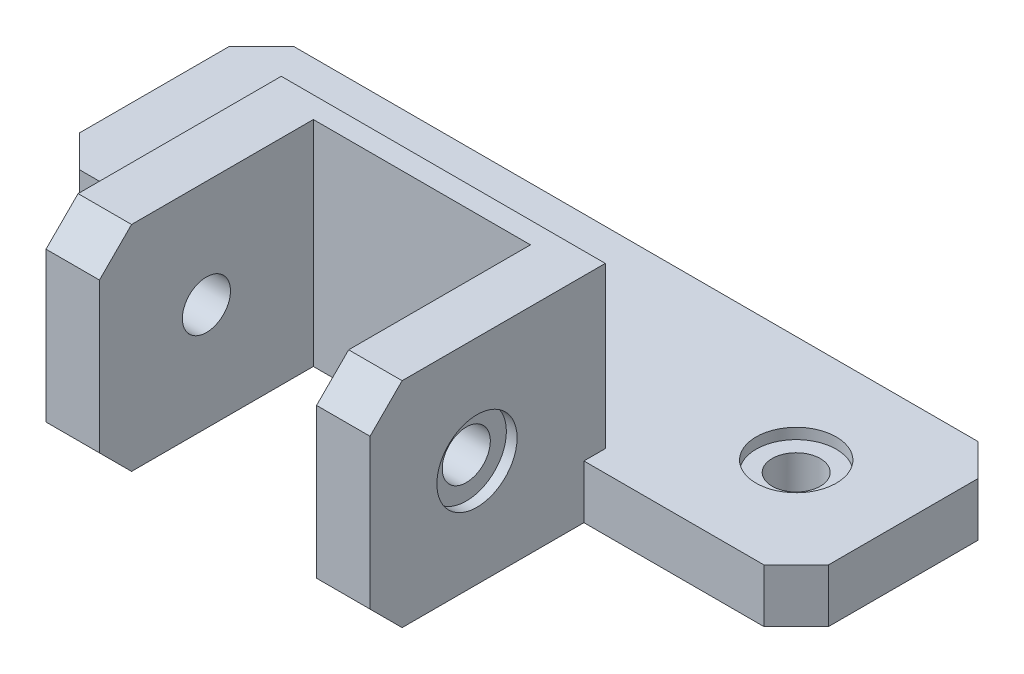
SolidWorks part; units mm, degrees
ref_plane "Front Plane" through (0, 0, 0) normal (0, 0, 1) x (1, 0, 0)
ref_plane "Top Plane" through (0, 0, 0) normal (0, 1, 0) x (1, 0, 0)
ref_plane "Right Plane" through (0, 0, 0) normal (1, 0, 0) x (0, 0, -1)
sketch "Sketch3" plane through (0, 0, 0) normal (0, 1, 0) x (1, 0, 0)
  line L1 (-35, -10) -> (35, -10)
  line L2 (-35, -10) -> (-35, 10)
  line L3 (-35, 10) -> (35, 10)
  line L4 (35, -10) -> (35, 10)
  line L5 (-35, -10) -> (35, 10) construction
  line L6 (-35, 10) -> (35, -10) construction
  point P0 (0, 0)
  dimension "D1" = 20
  dimension "D2" = 70
extrude "Boss-Extrude2" add sketch "Sketch3" along normal blind 5
sketch "Sketch4" plane through (0, 5, 0) normal (0, 1, 0) x (1, 0, 0)
  line L0 (0, 0) -> (0, -10) construction
  line L1 (-35, -10) -> (35, -10) construction
  line L2 (-15.15, -5) -> (15.15, -5)
  line L7 (15.15, -5) -> (15.15, -30)
  line L8 (10.15, -30) -> (15.15, -30)
  line L10 (-10.15, -10) -> (-10.15, -30)
  line L11 (-10.15, -30) -> (-15.15, -30)
  line L12 (-15.15, -5) -> (-15.15, -30)
  line L13 (10.15, -10) -> (10.15, -30)
  line L14 (10.15, -10) -> (-10.15, -10)
  point P7 (0, -5)
  dimension "D3" = 20
  dimension "D4" = 15.15
  dimension "D5" = 5
extrude "Boss-Extrude3" add sketch "Sketch4" against normal blind 5 and the other way blind 15
sketch "Sketch5" plane through (0, 5, 0) normal (0, 1, 0) x (1, 0, 0)
  line L0 (-35, 0) -> (35, 0) construction
  line L1 (-35, 10) -> (-35, -10) construction
  line L2 (35, -10) -> (35, 10) construction
  circle A0 centre (0, 0) radius 2.25
  circle A1 centre (25, 0) radius 2.25
  circle A2 centre (-25, 0) radius 2.25
  dimension "D1" = 4.5
  dimension "D4" = 25
  dimension "D5" = 25
  dimension "D2" = 2
  dimension "D3" = 2
extrude "Cut-Extrude1" cut sketch "Sketch5" against normal up to next
sketch "Sketch6" plane through (0, 5, 0) normal (0, 1, 0) x (1, 0, 0)
  circle A0 centre (-25, 0) radius 3.75
  circle A1 centre (0, 0) radius 3.75
  circle A2 centre (25, 0) radius 3.75
  dimension "D1" = 7.5
  dimension "D3" = 25
  dimension "D2" = 3
extrude "Cut-Extrude2" cut sketch "Sketch6" against normal blind 1 and the other way through all
sketch "Sketch7" plane through (-15.15, 0, 0) normal (-1, 0, 0) x (0, 0, 1)
  line L1 (30, 0) -> (10, 0) construction
  line L4 (20, 0) -> (20, 20) construction
  line L5 (5, 20) -> (30, 20) construction
  circle A0 centre (20, 10) radius 2.25
  dimension "D1" = 4.5
extrude "Cut-Extrude3" cut sketch "Sketch7" against normal through all and the other way through all
sketch "Sketch11" plane through (-15.15, 0, 0) normal (-1, 0, 0) x (0, 0, 1)
  circle A0 centre (20, 10) radius 3.75
  dimension "D1" = 7.5
extrude "Cut-Extrude4" cut sketch "Sketch11" against normal blind 1
sketch "Sketch12" plane through (15.15, 0, 0) normal (1, 0, 0) x (0, 0, -1)
  circle A0 centre (-20, 10) radius 3.75
  dimension "D1" = 7.5
extrude "Cut-Extrude5" cut sketch "Sketch12" against normal blind 1
chamfer "Chamfer1" distance 3 angle 45 11 edges at (15.15, 12.5, 5) (0, 20, 5) (-15.15, 12.5, 5) (-35, 2.5, 10) (-35, 2.5, -10) (35, 2.5, -10) (35, 2.5, 10) (12.65, 0, 30) (12.65, 20, 30) (-12.65, 0, 30) (-12.65, 20, 30)
